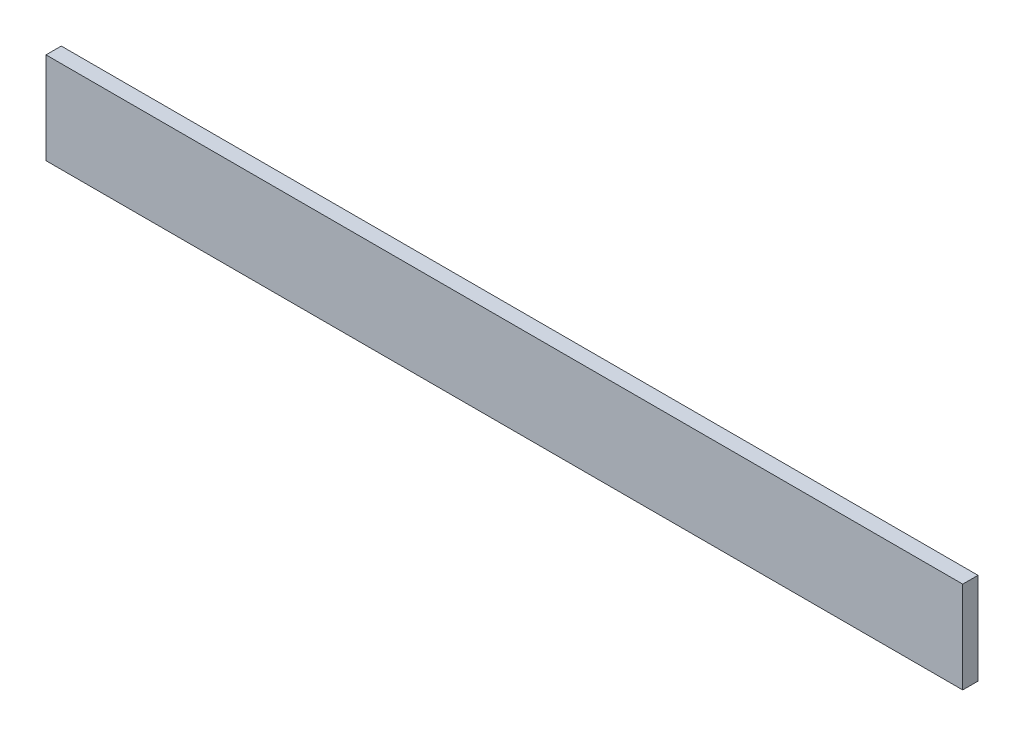
SolidWorks part; units mm, degrees
ref_plane "Front Plane" through (0, 0, 0) normal (0, 0, 1) x (1, 0, 0)
ref_plane "Top Plane" through (0, 0, 0) normal (0, 1, 0) x (1, 0, 0)
ref_plane "Right Plane" through (0, 0, 0) normal (1, 0, 0) x (0, 0, -1)
sketch "Sketch1" plane through (0, 0, 0) normal (0, 0, 1) x (1, 0, 0)
  line L1 (0, 0) -> (300, 0)
  line L2 (0, 0) -> (0, 30)
  line L3 (0, 30) -> (300, 30)
  line L4 (300, 0) -> (300, 30)
  dimension "D1" = 300
  dimension "D2" = 30
extrude "Boss-Extrude1" add sketch "Sketch1" along normal blind 5
